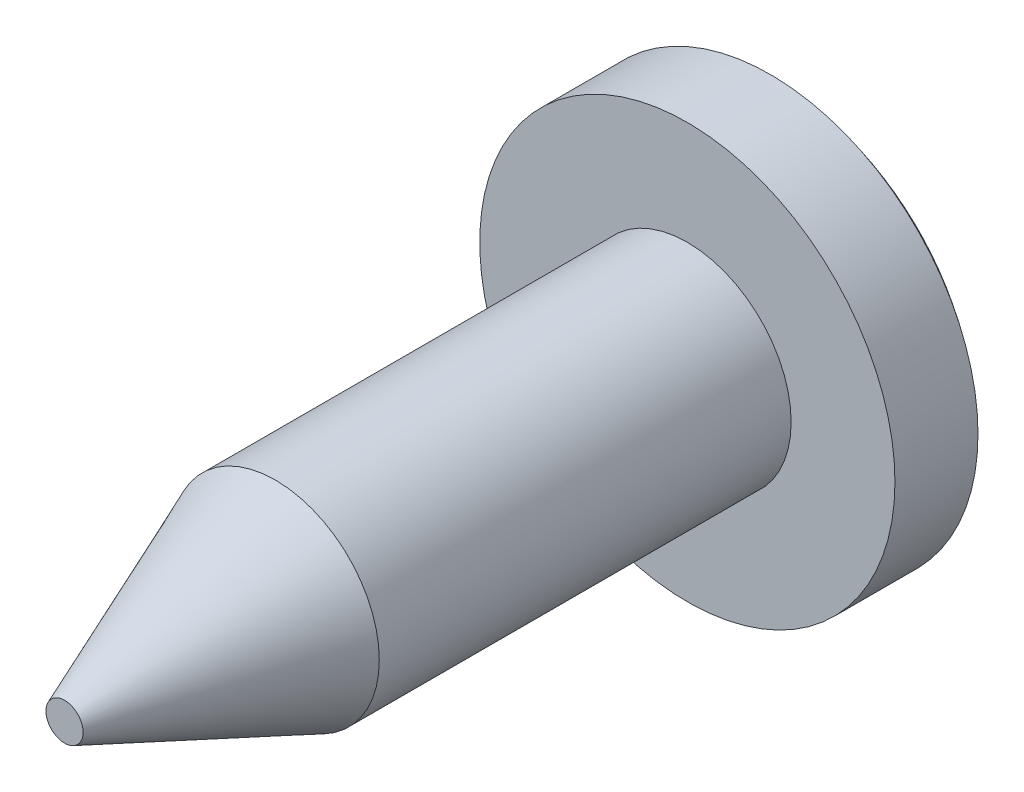
SolidWorks part; units mm, degrees
material "ASTM A36 Steel"
ref_plane "Front Plane" through (0, 0, 0) normal (0, 0, 1) x (1, 0, 0)
ref_plane "Top Plane" through (0, 0, 0) normal (0, 1, 0) x (1, 0, 0)
ref_plane "Right Plane" through (0, 0, 0) normal (1, 0, 0) x (0, 0, -1)
sketch "Sketch1" plane through (0, 0, 0) normal (0, 1, 0) x (1, 0, 0)
  line L0 (0, 0) -> (0, 7.5)
  line L1 (0, 0) -> (1, 0)
  line L2 (1, 0) -> (1, 6)
  line L3 (1, 6) -> (2, 6)
  line L4 (2, 6) -> (2, 6.8)
  line L5 (0, 7.5) -> (-1.075, 7.5) construction
  arc A0 (2, 6.8) -> (0, 7.5) centre (0, 4.2929) ccw
  dimension "D1" = 7.5
  dimension "D2" = 1
  dimension "D3" = 2
  dimension "D4" = 0.8
  dimension "D5" = 6
revolve "Revolve1" add sketch "Sketch1" angle 360 about L0
sketch "Sketch2" plane through (0, 0, 0) normal (0, 1, 0) x (1, 0, 0)
  line L0 (0, 6.8) -> (0, 0) construction
  line L1 (2, 6.8) -> (-2, 6.8) construction
  line L3 (0.3, 6.8) -> (-0.3, 6.8)
  line L4 (0.3, 6.8) -> (0.3, 8.3185)
  line L5 (0.3, 8.3185) -> (-0.3, 8.3185)
  line L6 (-0.3, 6.8) -> (-0.3, 8.3185)
  dimension "D1" = 0.6
extrude "Extrude1" cut sketch "Sketch2" against normal mid plane 2.54
sketch "Sketch3" plane through (0, 0, 0) normal (1, 0, 0) x (0, 0, -1)
  line L0 (0, 0) -> (6.8, 0) construction
  line L2 (6.8, 2) -> (6.8, -2) construction
  line L4 (6.8, 0.2945) -> (7.9032, 0.2945)
  line L5 (6.8, 0.2945) -> (6.8, -0.2945)
  line L6 (6.8, -0.2945) -> (7.9032, -0.2945)
  line L7 (7.9032, 0.2945) -> (7.9032, -0.2945)
extrude "Extrude2" cut sketch "Sketch3" against normal mid plane 2.54
chamfer "Chamfer1" distance 2.032 angle 22 1 edges at (1, 0, 0)
